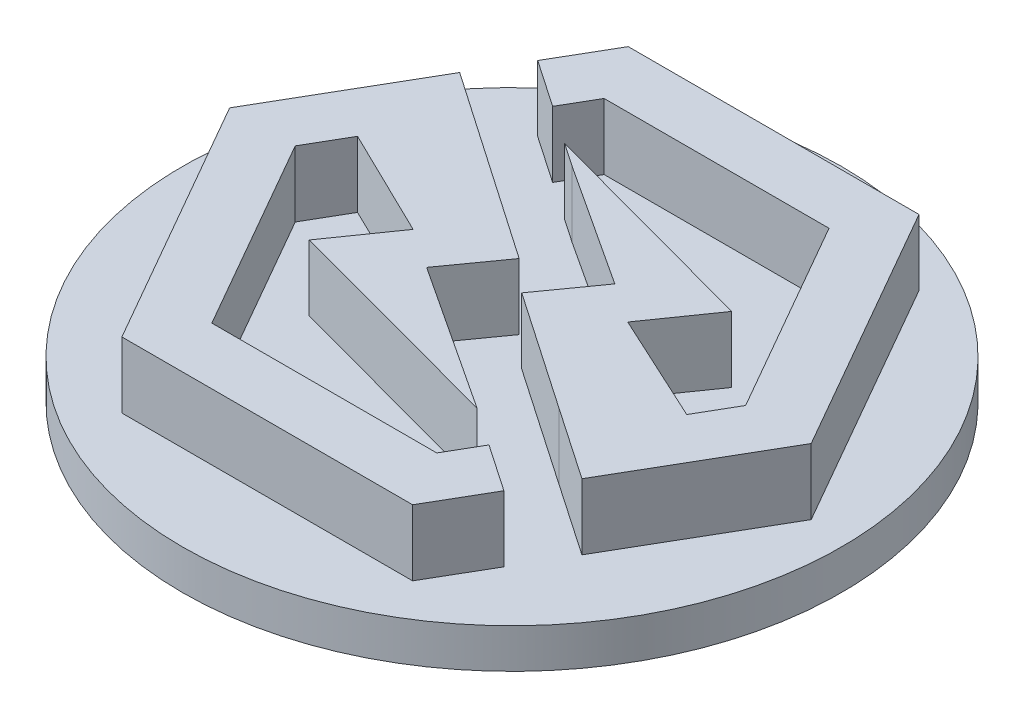
SolidWorks part; units mm, degrees
ref_plane "Ebene vorne" through (0, 0, 0) normal (0, 0, 1) x (1, 0, 0)
ref_plane "Ebene oben" through (0, 0, 0) normal (0, 1, 0) x (1, 0, 0)
ref_plane "Ebene rechts" through (0, 0, 0) normal (1, 0, 0) x (0, 0, -1)
sketch "Skizze2" plane through (0, 0, 0) normal (0, 1, 0) x (1, 0, 0)
  circle A0 centre (0, 0) radius 25
  dimension "D1" = 50
extrude "Aufsatz-Linear austragen2" add sketch "Skizze2" along normal blind 3
sketch "Model" plane through (0, 3, -3) normal (0, -1, 0) x (1, 0, 0)
  line L0 (-4.1045, 5.3713) -> (-1.1784, 1.2797)
  line L1 (-1.1784, 1.2797) -> (-15.6531, -8.6844)
  line L2 (-15.6531, -8.6844) -> (-22.0556, 2.3618)
  line L3 (-22.0556, 2.3618) -> (-11.0945, 21.4996)
  line L4 (-11.0945, 21.4996) -> (10.9599, 21.4974)
  line L5 (10.9599, 21.4974) -> (13.4998, 17.1151)
  line L6 (13.4998, 17.1151) -> (9.9242, 14.6693)
  line L7 (9.9242, 14.6693) -> (8.4704, 17.1776)
  line L8 (8.4704, 17.1776) -> (-8.5905, 17.1793)
  line L9 (-8.5905, 17.1793) -> (-17.0697, 2.3747)
  line L10 (-17.0697, 2.3747) -> (-15.3353, -0.6178)
  line L11 (-15.3353, -0.6178) -> (-7.1153, 3.3866)
  line L12 (-7.1153, 3.3866) -> (-10.3588, 8.0256)
  line L13 (-10.3588, 8.0256) -> (7.0505, 12.7038)
  line L14 (7.0505, 12.7038) -> (-4.1045, 5.3713)
  line L15 (15.672, 13.3672) -> (10.1698, 9.6036)
  line L16 (10.1698, 9.6036) -> (1.1764, 3.439)
  line L17 (1.1764, 3.439) -> (4.119, -0.6808)
  line L18 (4.119, -0.6808) -> (-5.2612, -6.8102)
  line L19 (-5.2612, -6.8102) -> (-7.0087, -8.0055)
  line L20 (-7.0087, -8.0055) -> (10.3569, -3.3069)
  line L21 (10.3569, -3.3069) -> (7.1133, 1.3321)
  line L22 (7.1133, 1.3321) -> (15.4283, 5.173)
  line L23 (15.4283, 5.173) -> (17.0677, 2.3442)
  line L24 (17.0677, 2.3442) -> (8.5885, -12.4607)
  line L25 (8.5885, -12.4607) -> (-8.4724, -12.4587)
  line L26 (-8.4724, -12.4587) -> (-9.9051, -9.9867)
  line L27 (-9.9051, -9.9867) -> (-13.4807, -12.4325)
  line L28 (-13.4807, -12.4325) -> (-10.9619, -16.7784)
  line L29 (-10.9619, -16.7784) -> (11.0926, -16.7809)
  line L30 (11.0926, -16.7809) -> (22.0533, 2.3571)
  line L31 (22.0533, 2.3571) -> (15.672, 13.3672)
extrude "Aufsatz-Linear austragen1" add sketch "Model" against normal blind 5
